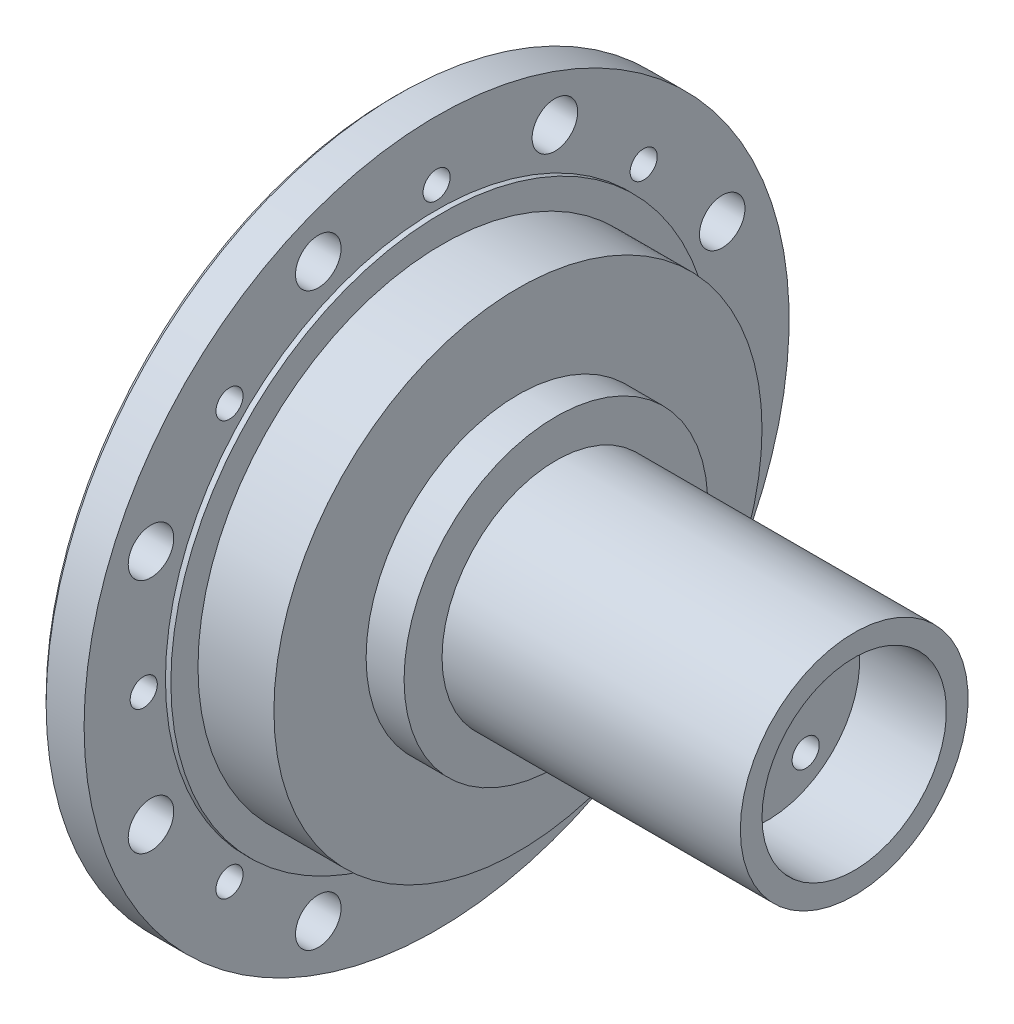
SolidWorks part; units mm, degrees
material "Ductile Iron"
ref_plane "Front Plane" through (0, 0, 0) normal (0, 0, 1) x (1, 0, 0)
ref_plane "Top Plane" through (0, 0, 0) normal (0, 1, 0) x (1, 0, 0)
ref_plane "Right Plane" through (0, 0, 0) normal (1, 0, 0) x (0, 0, -1)
sketch "Sketch1" plane through (0, 0, 0) normal (0, 0, -1) x (0, 1, 0)
  line L0 (0, 0) -> (0, 46.1914) construction
  line L1 (-32.5, -4.5) -> (-32.5, -0.5)
  line L3 (-32.5, -4.5) -> (-24, -4.5)
  line L4 (-24, -4.5) -> (-24, -7.5)
  line L5 (-24, -7.5) -> (-20, -7.5)
  line L9 (0, 30) -> (-8.5, 30)
  line L10 (-8.5, 30) -> (-8.5, 38)
  line L11 (-8.5, 38) -> (-10.5, 38)
  line L12 (-10.5, 38) -> (-10.5, 10.5)
  line L14 (-10.5, 10.5) -> (-14, 10.5)
  line L15 (-14, 10.5) -> (-14, 7)
  line L16 (-25, 0) -> (-22.5, 0)
  line L17 (-22.5, 0) -> (-22.5, 7)
  line L19 (-22.5, 7) -> (-14, 7)
  line L23 (-32.5, -0.5) -> (-25, -0.5)
  line L24 (-25, -0.5) -> (-25, 0)
  line L25 (-20, -7.5) -> (-20, 4.5)
  line L26 (-20, 4.5) -> (-8, 4.5)
  line L27 (-8, 4.5) -> (-8, 9.5)
  line L28 (-8, 9.5) -> (0, 9.5)
  line L29 (0, 9.5) -> (0, 30)
  point P17 (-9.5, 38)
  dimension "D2" = 3
  dimension "D3" = 12
  dimension "D4" = 2.5
  dimension "D5" = 17
  dimension "D6" = 2.5
  dimension "D7" = 4.5
  dimension "D8" = 5
  dimension "D9" = 8
  dimension "D10" = 10.5
  dimension "D11" = 14
  dimension "D12" = 3.5
  dimension "D13" = 27.5
  dimension "D14" = 32.5
  dimension "D15" = 45
  dimension "D16" = 7
  dimension "D17" = 24
  dimension "D18" = 20
  dimension "D19" = 50
  dimension "D20" = 0.5
revolve "Revolve1" add sketch "Sketch1" angle 360 about L0
sketch "Sketch2" plane through (-7.5, 0, 0) normal (-1, 0, 0) x (0, 0, 1)
  line L0 (-8.9443, 22) -> (8.9443, 22)
  line L1 (-22, 8.9443) -> (-22, -8.9443)
  line L2 (-8.9443, -22) -> (8.9443, -22)
  line L3 (22, 8.9443) -> (22, -8.9443)
  line L4 (-16.9706, 16.9706) -> (16.9706, -16.9706) construction
  line L5 (-16.9706, -16.9706) -> (16.9706, 16.9706) construction
  arc A0 (21.7143, 10.222) -> (10.222, 21.7143) centre (0, 0) ccw
  arc A1 (10.222, -21.7143) -> (21.7143, -10.222) centre (0, 0) ccw
  arc A2 (-21.7143, -10.222) -> (-10.222, -21.7143) centre (0, 0) ccw
  arc A3 (-10.222, 21.7143) -> (-21.7143, 10.222) centre (0, 0) ccw
  arc A4 (22, -8.9443) -> (21.7143, -10.222) centre (19, -8.9443) cw
  arc A5 (-8.9443, -22) -> (-10.222, -21.7143) centre (-8.9443, -19) cw
  arc A6 (-22, 8.9443) -> (-21.7143, 10.222) centre (-19, 8.9443) cw
  arc A7 (8.9443, 22) -> (10.222, 21.7143) centre (8.9443, 19) cw
  arc A8 (22, 8.9443) -> (21.7143, 10.222) centre (19, 8.9443) ccw
  arc A9 (-8.9443, 22) -> (-10.222, 21.7143) centre (-8.9443, 19) ccw
  arc A10 (8.9443, -22) -> (10.222, -21.7143) centre (8.9443, -19) ccw
  arc A11 (-22, -8.9443) -> (-21.7143, -10.222) centre (-19, -8.9443) ccw
  circle A14 centre (0, 0) radius 32.5 construction
  circle A15 centre (0, 0) radius 32.5
  point P0 (0, 0)
  dimension "D5" = 3
  dimension "D6" = 24
  dimension "D1" = 44
  dimension "D2" = 44
  dimension "D3" = 22
  dimension "D4" = 22
extrude "Cut-Extrude1" cut sketch "Sketch2" against normal up to surface (3 mm away) up to face at (-4.5, 0, 24)
sketch "Sketch3" plane through (30, 0, 0) normal (1, 0, 0) x (0, 0, -1)
  line L0 (0, 0) -> (0, 6) construction
  circle A0 centre (0, 6) radius 1.25
  circle A1 centre (5.7063, 1.8541) radius 1.25
  circle A2 centre (3.5267, -4.8541) radius 1.25
  circle A3 centre (-3.5267, -4.8541) radius 1.25
  circle A4 centre (-5.7063, 1.8541) radius 1.25
  point P14 (0, 0)
  dimension "D2" = 2.5
  dimension "D1" = 6
  dimension "D3" = 5
extrude "Cut-Extrude2" cut sketch "Sketch3" against normal blind 12
sketch "Sketch4" plane through (-4.5, 0, 0) normal (-1, 0, 0) x (0, 0, 1)
  line L0 (0, 0) -> (0, 27) construction
  line L1 (0, 0) -> (10.9065, 26.3306) construction
  circle A0 centre (0, 27) radius 1.25
  circle A1 centre (10.9065, 26.3306) radius 2.1
  circle A2 centre (19.0919, 19.0919) radius 1.25
  circle A3 centre (26.3306, 10.9065) radius 2.1
  circle A4 centre (27, 0) radius 1.25
  circle A5 centre (26.3306, -10.9065) radius 2.1
  circle A6 centre (19.0919, -19.0919) radius 1.25
  circle A7 centre (10.9065, -26.3306) radius 2.1
  circle A8 centre (0, -27) radius 1.25
  circle A9 centre (-10.9065, -26.3306) radius 2.1
  circle A10 centre (-19.0919, -19.0919) radius 1.25
  circle A11 centre (-26.3306, -10.9065) radius 2.1
  circle A12 centre (-27, 0) radius 1.25
  circle A13 centre (-26.3306, 10.9065) radius 2.1
  circle A14 centre (-19.0919, 19.0919) radius 1.25
  circle A15 centre (-10.9065, 26.3306) radius 2.1
  point P36 (0, 0)
  dimension "D2" = 2.5
  dimension "D5" = 4.2
  dimension "D6" = 8
  dimension "D1" = 27
  dimension "D3" = 28.5
  dimension "D4" = 22.5
extrude "Cut-Extrude3" cut sketch "Sketch4" against normal up to next
chamfer "Chamfer1" distance 0.5 angle 45 17 edges at (-7.5, -22, 0) (-7.5, -21.9277, -9.5989) (-7.5, -16.9706, -16.9706) (-7.5, -9.5989, -21.9277) (-7.5, 0, -22) (-7.5, 9.5989, -21.9277) (-7.5, 16.9706, -16.9706) (-7.5, 21.9277, -9.5989) (-7.5, 22, 0) (-7.5, 21.9277, 9.5989) (-7.5, 16.9706, 16.9706) (-7.5, 9.5989, 21.9277) (-7.5, 0, 22) (-7.5, -9.5989, 21.9277) (-7.5, -16.9706, 16.9706) (-7.5, -21.9277, 9.5989) (-7.5, 0, 20)
chamfer "Chamfer2" distance 0.5 angle 45 1 edges at (-4.5, 0, 32.5)
